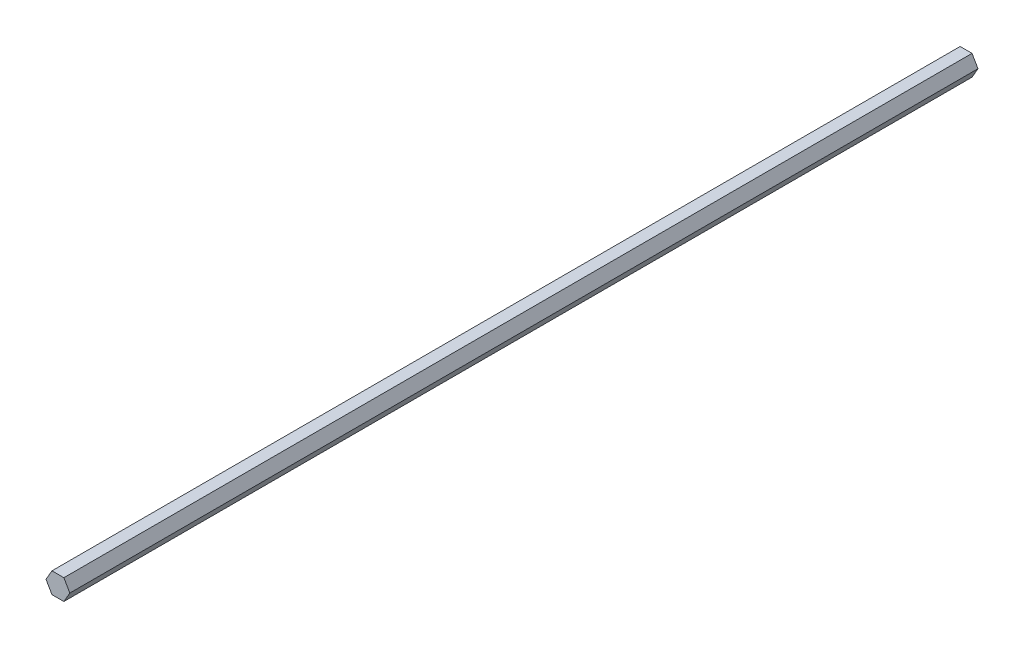
SolidWorks part; units mm, degrees
material "7075-O (SS)"
ref_plane "Front Plane" through (0, 0, 0) normal (0, 0, 1) x (1, 0, 0)
ref_plane "Top Plane" through (0, 0, 0) normal (0, 1, 0) x (1, 0, 0)
ref_plane "Right Plane" through (0, 0, 0) normal (1, 0, 0) x (0, 0, -1)
sketch "Sketch1" plane through (0, 0, 0) normal (0, 0, 1) x (1, 0, 0)
  line L1 (3.6662, -6.35) -> (7.3323, 0)
  line L2 (7.3323, 0) -> (3.6662, 6.35)
  line L3 (3.6662, 6.35) -> (-3.6662, 6.35)
  line L4 (-3.6662, 6.35) -> (-7.3323, 0)
  line L5 (-7.3323, 0) -> (-3.6662, -6.35)
  line L6 (-3.6662, -6.35) -> (3.6662, -6.35)
  circle A0 centre (0, 0) radius 6.35 construction
  dimension "D1" = 12.7
extrude "Boss-Extrude1" add sketch "Sketch1" along normal blind 558.8
